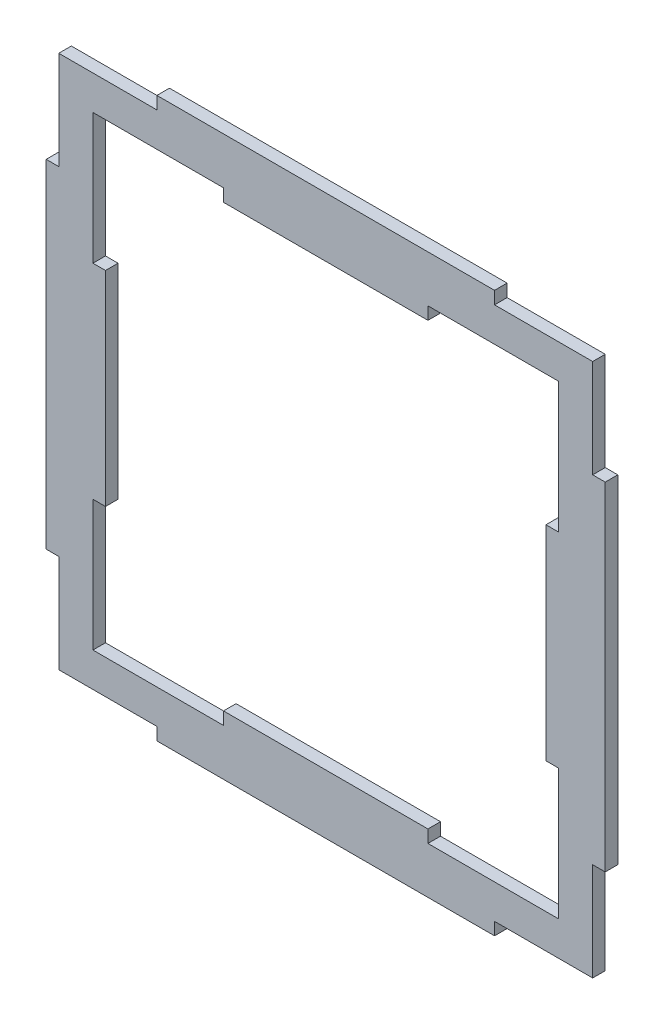
SolidWorks part; units mm, degrees
ref_plane "Front Plane" through (0, 0, 0) normal (0, 0, 1) x (1, 0, 0)
ref_plane "Top Plane" through (0, 0, 0) normal (0, 1, 0) x (1, 0, 0)
ref_plane "Right Plane" through (0, 0, 0) normal (1, 0, 0) x (0, 0, -1)
sketch "Sketch1" plane through (0, 0, 0) normal (0, 0, 1) x (1, 0, 0)
  line L0 (147.4, 61.7836) -> (152, 61.7836)
  line L1 (-48, -97.7) -> (-12.0836, -97.7)
  line L2 (-48, -97.7) -> (-48, -61.7836)
  line L3 (-48, 97.7) -> (-12.0836, 97.7)
  line L4 (147.4, -97.7) -> (147.4, -61.7836)
  line L7 (152, 61.7836) -> (152, -61.7836)
  line L8 (-12.0836, 97.7) -> (-12.0836, 102.3)
  line L9 (-12.0836, 102.3) -> (111.4836, 102.3)
  line L10 (111.4836, 97.7) -> (111.4836, 102.3)
  line L11 (147.4, 61.7836) -> (147.4, 97.7)
  line L12 (111.4836, -97.7) -> (147.4, -97.7)
  line L13 (147.4, -61.7836) -> (152, -61.7836)
  line L14 (111.4836, -97.7) -> (111.4836, -102.3)
  line L15 (111.4836, -102.3) -> (-12.0836, -102.3)
  line L16 (-12.0836, -97.7) -> (-12.0836, -102.3)
  line L17 (-48, -61.7836) -> (-52.6, -61.7836)
  line L18 (-52.6, -61.7836) -> (-52.6, 61.7836)
  line L19 (-48, 61.7836) -> (-52.6, 61.7836)
  line L20 (-48, 61.7836) -> (-48, 97.7)
  line L21 (111.4836, 97.7) -> (147.4, 97.7)
  point P0 (49.7, 0)
  point P6 (0, 48)
  dimension "D1" = 195.4
  dimension "D2" = 195.4
  dimension "D3" = 4.6
  dimension "D4" = 4
extrude "Boss-Extrude1" add sketch "Sketch1" along normal blind 4.6
sketch "Sketch2" plane through (0, 0, 0) normal (0, 0, -1) x (-1, 0, 0)
  line L0 (-49.7, 102.3) -> (-49.7, -80.6) construction
  line L1 (-111.4836, 102.3) -> (12.0836, 102.3) construction
  line L3 (52.6, 0) -> (44.7034, 0) construction
  line L4 (52.6, 61.7836) -> (52.6, -61.7836) construction
  line L6 (30.9, 0) -> (-130.3, 0) construction
  line L7 (-134.9, -85.2) -> (-87.1087, -85.2)
  line L8 (-134.9, -85.2) -> (-134.9, -37.4087)
  line L9 (-134.9, 85.2) -> (-87.1087, 85.2)
  line L10 (35.5, -85.2) -> (35.5, -37.4087)
  line L11 (-134.9, -85.2) -> (35.5, 85.2) construction
  line L12 (-134.9, 85.2) -> (35.5, -85.2) construction
  line L13 (35.5, -37.4087) -> (30.9, -37.4087)
  line L14 (35.5, 37.4087) -> (35.5, 85.2)
  line L15 (35.5, 37.4087) -> (30.9, 37.4087)
  line L16 (30.9, -37.4087) -> (30.9, 37.4087)
  line L17 (-87.1087, -80.6) -> (-12.2913, -80.6)
  line L18 (-12.2913, -85.2) -> (-12.2913, -80.6)
  line L19 (-87.1087, -85.2) -> (-87.1087, -80.6)
  line L20 (-130.3, 37.4087) -> (-130.3, -37.4087)
  line L21 (-134.9, -37.4087) -> (-130.3, -37.4087)
  line L22 (-134.9, 37.4087) -> (-130.3, 37.4087)
  line L23 (-12.2913, 80.6) -> (-87.1087, 80.6)
  line L24 (-87.1087, 85.2) -> (-87.1087, 80.6)
  line L25 (-12.2913, 85.2) -> (-12.2913, 80.6)
  line L26 (-12.2913, 85.2) -> (35.5, 85.2)
  line L27 (-134.9, 37.4087) -> (-134.9, 85.2)
  line L28 (-12.2913, -85.2) -> (35.5, -85.2)
  point P1 (-168.1352, 117.5893)
  point P13 (-49.7, 0)
  point P18 (35.5, 0)
  dimension "D1" = 170.4
  dimension "D2" = 170.4
  dimension "D3" = 4.6
extrude "Cut-Extrude1" cut sketch "Sketch2" against normal through all
equation "\"mat\"=\"mat@levv1.assembly\""
equation "\"D3@Sketch1\" = \"mat\""
equation "\"D1@Boss-Extrude1\"=\"mat\""
equation "\"D1@Sketch2\" = 175-\"mat\""
equation "\"D2@Sketch2\" = 175-\"mat\""
equation "\"D3@Sketch2\" = \"mat\""
equation "\"D1@Sketch1\" = 200-\"mat\""
equation "\"D2@Sketch1\"=200-\"mat\""
